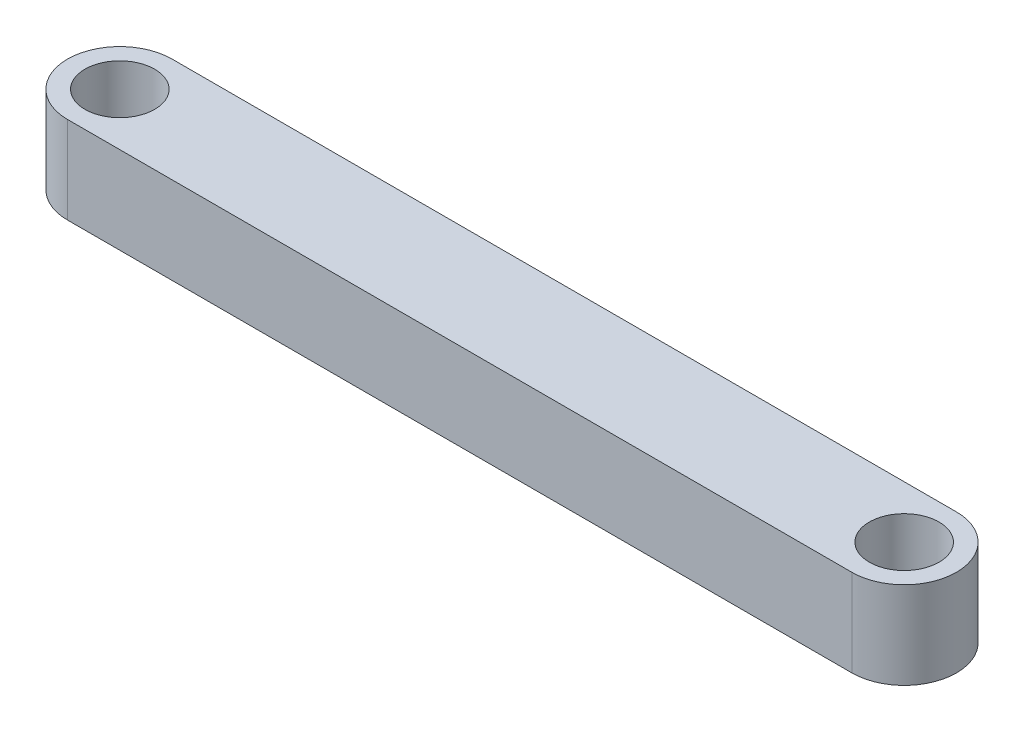
SolidWorks part; units mm, degrees
ref_plane "Front Plane" through (0, 0, 0) normal (0, 0, 1) x (1, 0, 0)
ref_plane "Top Plane" through (0, 0, 0) normal (0, 1, 0) x (1, 0, 0)
ref_plane "Right Plane" through (0, 0, 0) normal (1, 0, 0) x (0, 0, -1)
sketch "Sketch1" plane through (0, 0, 0) normal (0, 1, 0) x (1, 0, 0)
  line L0 (-22.5, 0) -> (22.5, 0) construction
  line L1 (-22.5, 3) -> (22.5, 3)
  line L2 (-22.5, -3) -> (22.5, -3)
  arc A0 (-22.5, 3) -> (-22.5, -3) centre (-22.5, 0) ccw
  arc A1 (22.5, -3) -> (22.5, 3) centre (22.5, 0) ccw
  circle A2 centre (-22.5, 0) radius 2
  circle A3 centre (22.5, 0) radius 2
  point P3 (0, 0)
  dimension "D3" = 4
  dimension "D4" = 4
  dimension "D1" = 45
  dimension "D2" = 6
extrude "Boss-Extrude1" add sketch "Sketch1" along normal blind 5
